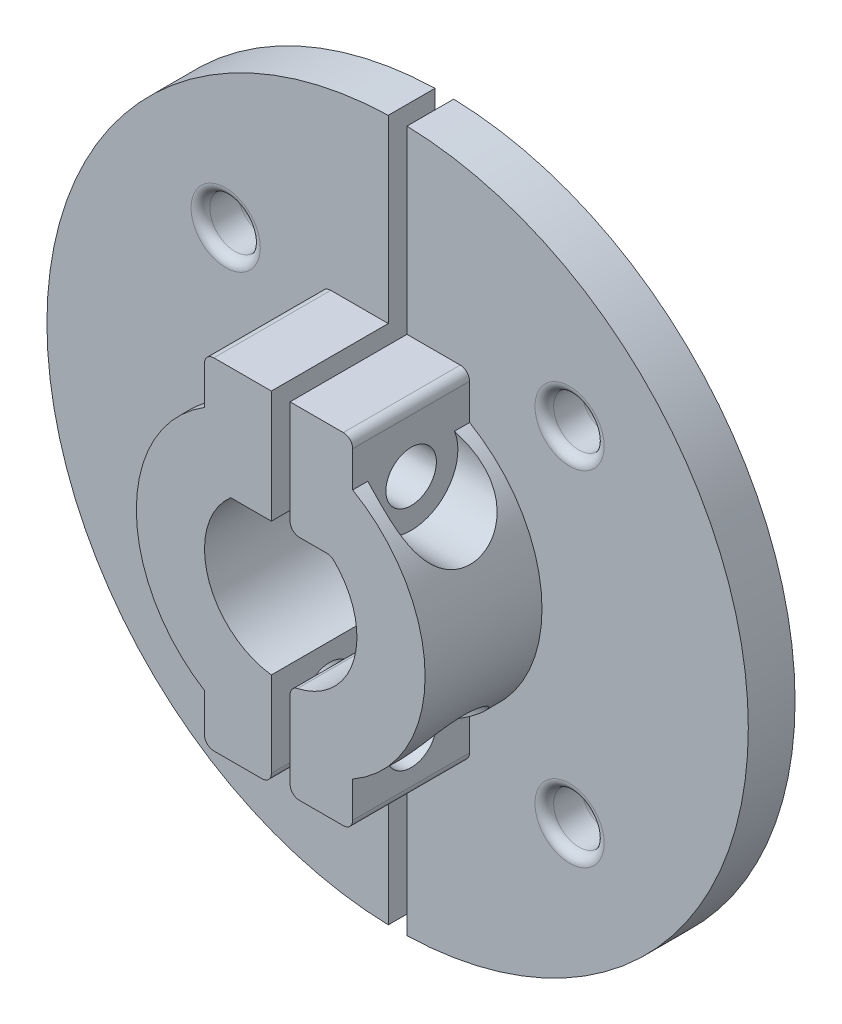
SolidWorks part; units mm, degrees
ref_plane "Front Plane" through (0, 0, 0) normal (0, 0, 1) x (1, 0, 0)
ref_plane "Top Plane" through (0, 0, 0) normal (0, 1, 0) x (1, 0, 0)
ref_plane "Right Plane" through (0, 0, 0) normal (1, 0, 0) x (0, 0, -1)
sketch "Sketch1" plane through (0, 0, 0) normal (0, 0, 1) x (1, 0, 0)
  line L1 (0, 0) -> (37.5, 0) construction
  line L2 (20.294, 20.294) -> (16.4756, 16.4756) construction
  circle A7 centre (0, 0) radius 37.5
  circle A8 centre (0, 0) radius 8.15
  circle A15 centre (18.3848, 18.3848) radius 2.7
  circle A16 centre (-18.3848, 18.3848) radius 2.7
  circle A17 centre (-18.3848, -18.3848) radius 2.7
  circle A18 centre (18.3848, -18.3848) radius 2.7
  point P8 (16.4756, 16.4756)
  point P11 (26.5165, 26.5165)
  dimension "D1" = 75
  dimension "D2" = 16.3
  dimension "D3" = 5.4
  dimension "D7" = 26
  dimension "D5" = 26
  dimension "D6" = 5.4
  dimension "D4" = 45
extrude "Boss-Extrude1" add sketch "Sketch1" along normal blind 17.5
sketch "Sketch2" plane through (0, 0, 17.5) normal (0, 0, 1) x (1, 0, 0)
  circle A0 centre (0, 0) radius 15.44
  dimension "D1" = 30.88
extrude "Cut-Extrude1" cut sketch "Sketch2" against normal blind 12.5 flip side to cut
sketch "Sketch5" plane through (0, 0, 5) normal (0, 0, 1) x (1, 0, 0)
  line L5 (7.6946, 18.2027) -> (7.6946, 12.2027)
  line L6 (-8.15, 12.2027) -> (7.6946, 12.2027)
  line L9 (-8.15, 12.2027) -> (-8.15, 18.2027)
  line L10 (-8.15, 18.2027) -> (7.6946, 18.2027)
  line L11 (0, 0) -> (31.0751, 0) construction
  line L13 (-8.15, 12.2027) -> (7.6946, 12.2027)
  line L15 (7.6946, 12.2027) -> (7.6946, 18.2027)
  line L16 (-8.15, -18.2027) -> (7.6946, -18.2027)
  line L17 (7.6946, -12.2027) -> (7.6946, -18.2027)
  line L18 (-8.15, -12.2027) -> (7.6946, -12.2027)
  line L19 (-8.15, -12.2027) -> (-8.15, -18.2027)
  point P0 (0, 0)
  circle M5 centre (0, 0) radius 15.44
  dimension "D1" = 6
extrude "Boss-Extrude6" add sketch "Sketch5" along normal blind 12.5 contours L10 L9 L5 M5 | L19 L16 L17 M5
sketch "Sketch14" plane through (0, 0, 0) normal (0, 0, -1) x (-1, 0, 0)
  line L0 (0, 6.15) -> (5.3479, 6.15)
  line L1 (0, 6.15) -> (-5.3479, 6.15)
  circle A0 centre (0, 0) radius 8.15
  point P3 (0, 6.15)
  point P4 (0, 8.15)
  circle M2 centre (0, 0) radius 8.15
  dimension "D1" = 2
extrude "Boss-Extrude7" add sketch "Sketch14" against normal blind 17.5 contours L1 L0 M2
sketch "Sketch15" plane through (0, 0, 17.5) normal (0, 0, 1) x (1, 0, 0)
  line L1 (1, -40.939) -> (-1, -40.939)
  line L2 (1, -40.939) -> (1, 40.939)
  line L3 (1, 40.939) -> (-1, 40.939)
  line L4 (-1, -40.939) -> (-1, 40.939)
  line L5 (1, -40.939) -> (-1, 40.939) construction
  line L6 (1, 40.939) -> (-1, -40.939) construction
  point P0 (0, 0)
extrude "Cut-Extrude9" cut sketch "Sketch15" against normal through all both and the other way through all
sketch "Sketch16" plane through (7.6946, 0, 0) normal (1, 0, 0) x (0, 0, -1)
  line L0 (-11.25, 18.2027) -> (-11.25, 37.4029) construction
  line L1 (-17.5, 18.2027) -> (-5, 18.2027) construction
  line L2 (-11.25, 18.2027) -> (-11.25, -25.1309) construction
  line L3 (0, 0) -> (-31.6399, 0) construction
  line L4 (0, -37.4867) -> (0, 37.4867) construction
  circle A0 centre (-11.25, 11.5128) radius 2.7
  circle A1 centre (-11.25, -12.7446) radius 2.7
  point P9 (-11.25, 6.15)
  dimension "D2" = 5.4
  dimension "D3" = 5.4
  dimension "D1" = 6.15
extrude "Cut-Extrude10" cut sketch "Sketch16" against normal through all both and the other way through all
sketch "Sketch17" plane through (-8.15, 0, 0) normal (-1, 0, 0) x (0, 0, 1)
  circle A0 centre (11.25, 11.5128) radius 5
  circle A1 centre (11.25, -12.7446) radius 5
extrude "Cut-Extrude11" cut sketch "Sketch17" along normal through all
sketch "Sketch19" plane through (7.6946, 0, 0) normal (1, 0, 0) x (0, 0, -1)
  circle A0 centre (-11.25, 11.5128) radius 5
  circle A1 centre (-11.25, -12.7446) radius 5
extrude "Cut-Extrude12" cut sketch "Sketch19" along normal through all
fillet "Fillet1" radius 1 10 edges at (21.0848, -18.3848, 5) (15.6848, -18.3848, 0) (21.0848, 18.3848, 5) (21.0848, 18.3848, 0) (1, 6.15, 8.75) (5.3479, 6.15, 8.75) (1, -8.0884, 8.75) (1, -18.2027, 11.25) (7.6946, -18.2027, 11.25) (7.6946, 18.2027, 11.25)
fillet "Fillet2" radius 1 7 edges at (-15.6848, -18.3848, 0) (-21.0848, 18.3848, 0) (-1, -18.2027, 11.25) (-8.15, -18.2027, 11.25) (-15.6848, 18.3848, 5) (-15.6848, -18.3848, 5) (-8.15, 18.2027, 11.25)
